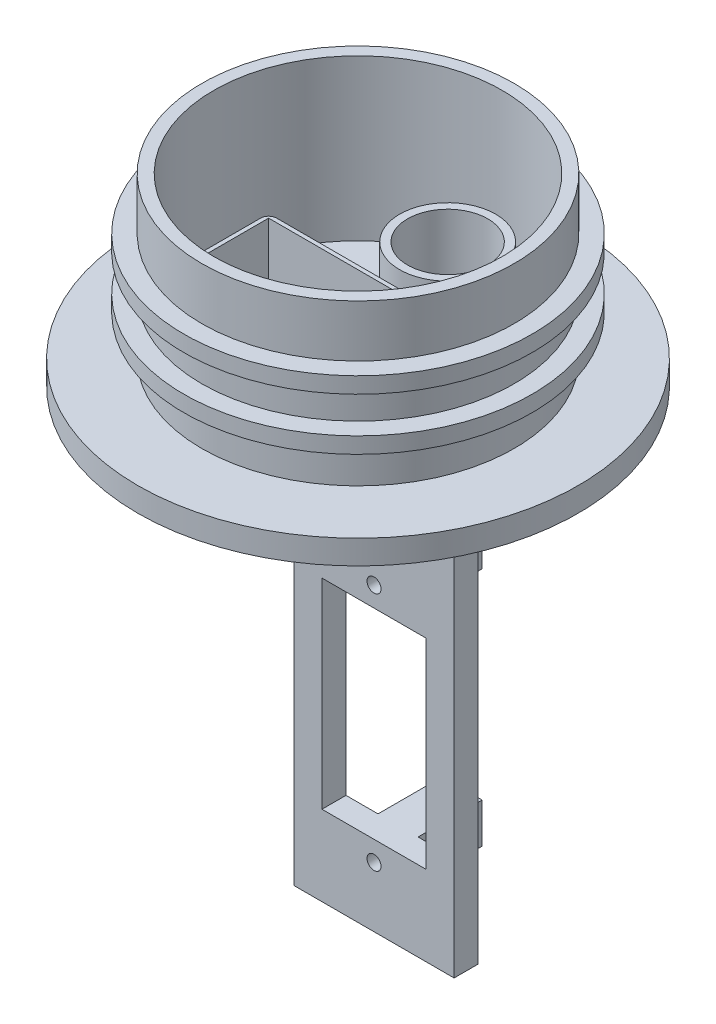
SolidWorks part; units mm, degrees
ref_plane "前基準面" through (0, 0, 0) normal (0, 0, 1) x (1, 0, 0)
ref_plane "上基準面" through (0, 0, 0) normal (0, 1, 0) x (1, 0, 0)
ref_plane "右基準面" through (0, 0, 0) normal (1, 0, 0) x (0, 0, -1)
sketch "草圖1" plane through (0, 0, 0) normal (0, 1, 0) x (1, 0, 0)
  circle A0 centre (0, 0) radius 19.5
  circle A1 centre (0, 0) radius 18
  dimension "D1" = 39
  dimension "D2" = 36
extrude "填料-伸長1" add sketch "草圖1" along normal blind 20
sketch "草圖3" plane through (0, 0, 0) normal (0, -1, 0) x (1, 0, 0)
  circle A0 centre (0, 0) radius 27.5
  dimension "D1" = 55
extrude "填料-伸長2" add sketch "草圖3" along normal blind 3
sketch "草圖4" plane through (0, 0, 0) normal (0, 0, 1) x (1, 0, 0)
  line L0 (0, 20) -> (0, -52.6673) construction
  line L1 (18, 20) -> (-18, 20) construction
  line L2 (-27.5, -3) -> (27.5, -3) construction
  line L3 (-10, -3) -> (10, -3)
  line L4 (-10, -3) -> (-10, -63)
  line L5 (-10, -63) -> (10, -63)
  line L6 (10, -3) -> (10, -63)
  line L8 (-6.5, -28) -> (6.5, -28)
  line L9 (-6.5, -28) -> (-6.5, -53)
  line L10 (-6.5, -53) -> (6.5, -53)
  line L11 (6.5, -28) -> (6.5, -53)
  dimension "D1" = 10
  dimension "D2" = 10
  dimension "D3" = 60
  dimension "D4" = 6.5
  dimension "D5" = 6.5
  dimension "D6" = 25
  dimension "D7" = 25
ref_plane "平面2" through (0, -3, 0) normal (0, -1, 0) x (-1, 0, 0)
sketch "草圖10" plane through (0, -3, 0) normal (0, -1, 0) x (-1, 0, 0)
  circle A0 centre (0, 11.196) radius 5
  circle A1 centre (0, 11.196) radius 6
  dimension "D1" = 10
  dimension "D2" = 12
extrude "填料-伸長6" add sketch "草圖10" against normal blind 10
sketch "草圖11" plane through (0, -3, 0) normal (0, -1, 0) x (-1, 0, 0)
  circle A0 centre (0, 11.196) radius 5.0075
extrude "除料-伸長4" cut sketch "草圖11" along normal blind 19 and the other way blind 10
sketch "草圖12" plane through (0, -3, 0) normal (0, -1, 0) x (1, 0, 0)
  line L0 (0, 18) -> (0, -18) construction
  line L2 (-10.75, 13.408) -> (10.75, 13.408)
  line L3 (-10.75, 13.408) -> (-10.75, 0.408)
  line L4 (-10.75, 0.408) -> (10.75, 0.408)
  line L5 (10.75, 13.408) -> (10.75, 0.408)
  circle A0 centre (0, 0) radius 18 construction
  dimension "D1" = 21.5
  dimension "D2" = 13
  dimension "D3" = 10.75
ref_plane "平面4" through (0, 0, -3) normal (0, 0, 1) x (1, 0, 0)
sketch "草圖15" plane through (0, 0, -3) normal (0, 0, 1) x (1, 0, 0)
  line L0 (0, 20) -> (0, -63) construction
  line L1 (-10, -3) -> (10, -3)
  line L2 (-10, -3) -> (-10, -63)
  line L3 (-10, -63) -> (10, -63)
  line L4 (10, -3) -> (10, -63)
  line L5 (-6.5, -28) -> (6.5, -28)
  line L6 (-6.5, -28) -> (-6.5, -53)
  line L7 (-6.5, -53) -> (6.5, -53)
  line L8 (6.5, -28) -> (6.5, -53)
  dimension "D1" = 60
  dimension "D2" = 25
  dimension "D3" = 13
extrude "填料-伸長7" add sketch "草圖15" along normal blind 1 and the other way blind 2
sketch "草圖16" plane through (0, 0, -3) normal (0, 0, 1) x (1, 0, 0)
  line L0 (-6.5, -28) -> (6.5, -28) construction
  line L1 (-2.5, -28) -> (2.5, -28)
  line L2 (-2.5, -28) -> (-2.5, -23)
  line L3 (-2.5, -23) -> (2.5, -23)
  line L4 (2.5, -28) -> (2.5, -23)
  line L5 (-6.5, -53) -> (6.5, -53) construction
  line L6 (-2.5, -53) -> (2.5, -53)
  line L7 (-2.5, -53) -> (-2.5, -58)
  line L8 (-2.5, -58) -> (2.5, -58)
  line L9 (2.5, -53) -> (2.5, -58)
  line L10 (0, 20) -> (0, -52.6673) construction
  dimension "D1" = 5
  dimension "D2" = 5
  dimension "D3" = 2.5
  dimension "D4" = 5
  dimension "D5" = 5
  dimension "D6" = 2.5
extrude "填料-伸長8" add sketch "草圖16" against normal blind 10
sketch "草圖18" plane through (0, 0, 0) normal (0, 0, 1) x (1, 0, 0)
  line L0 (-2.5, -25.5) -> (2.5, -25.5) construction
  line L1 (-2.5, -28) -> (-2.5, -23) construction
  line L2 (2.5, -28) -> (2.5, -23) construction
  line L3 (-2.5, -55.5) -> (2.5, -55.5) construction
  line L4 (-2.5, -53) -> (-2.5, -58) construction
  line L5 (2.5, -53) -> (2.5, -58) construction
  circle A0 centre (0, -55.5) radius 0.875
  circle A1 centre (0, -25.5) radius 0.875
  dimension "D1" = 1.75
  dimension "D2" = 1.75
extrude "除料-伸長5" cut sketch "草圖18" against normal blind 39 and the other way blind 10
extrude "除料-伸長6" cut sketch "草圖12" against normal blind 21.5 contours L5 L4 L3 L2
ref_plane "平面5" through (0, 0, 0) normal (0, 1, 0) x (1, 0, 0)
sketch "草圖19" plane through (0, 0, 0) normal (0, 1, 0) x (1, 0, 0)
  line L0 (-10.75, -13.408) -> (10.75, -13.408) construction
  line L1 (-11.25, 0.092) -> (11.25, 0.092)
  line L2 (-11.25, 0.092) -> (-11.25, -13.908)
  line L3 (-11.25, -13.908) -> (11.25, -13.908)
  line L4 (11.25, 0.092) -> (11.25, -13.908)
  line L5 (-10.75, -13.408) -> (-10.75, -0.408) construction
  line L6 (10.75, -13.408) -> (10.75, -0.408) construction
  line L8 (-10.75, -0.408) -> (10.75, -0.408) construction
  line L10 (-10.75, -0.408) -> (10.75, -0.408)
  line L11 (-10.75, -0.408) -> (-10.75, -13.408)
  line L12 (-10.75, -13.408) -> (10.75, -13.408)
  line L13 (10.75, -0.408) -> (10.75, -13.408)
  dimension "D1" = 0.5
  dimension "D2" = 0.5
  dimension "D3" = 0.5
  dimension "D4" = 0.5
extrude "填料-伸長9" add sketch "草圖19" along normal blind 10
fillet "圓角2" radius 1 1 edges at (-11.25, 5, -0.092)
fillet "圓角3" radius 1 1 edges at (11.25, 5, -0.092)
fillet "圓角4" radius 1 1 edges at (11.25, 5, 13.908)
fillet "圓角5" radius 1 1 edges at (-11.25, 5, 13.908)
ref_plane "平面6" through (0, 7, 0) normal (0, -1, 0) x (-1, 0, 0)
sketch "草圖25" plane through (0, 7, 0) normal (0, -1, 0) x (-1, 0, 0)
  circle A0 centre (0, 0) radius 21.75
  circle A1 centre (0, 0) radius 19.5
  dimension "D1" = 43.5
extrude "填料-伸長12" add sketch "草圖25" along normal blind 2
ref_plane "平面10" through (0, 10.5, 0) normal (0, -1, 0) x (-1, 0, 0)
sketch "草圖26" plane through (0, 10.5, 0) normal (0, -1, 0) x (-1, 0, 0)
  circle A0 centre (0, 0) radius 21.75
  circle A1 centre (0, 0) radius 19.5
extrude "填料-伸長13" add sketch "草圖26" against normal blind 2 from offset 1
